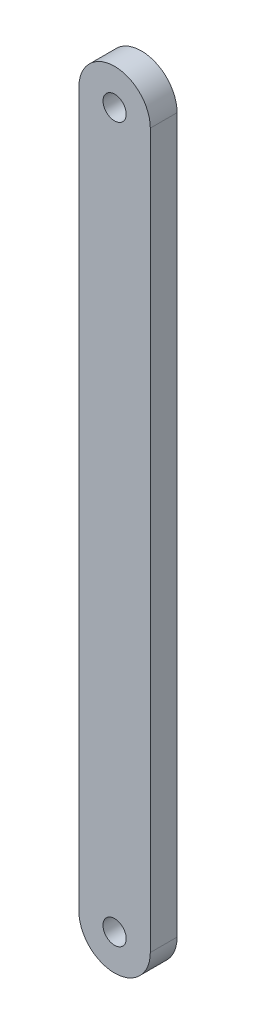
SolidWorks part; units mm, degrees
ref_plane "Front Plane" through (0, 0, 0) normal (0, 0, 1) x (1, 0, 0)
ref_plane "Top Plane" through (0, 0, 0) normal (0, 1, 0) x (1, 0, 0)
ref_plane "Right Plane" through (0, 0, 0) normal (1, 0, 0) x (0, 0, -1)
sketch "Model" plane through (0, 0, 0) normal (0, 0, 1) x (1, 0, 0)
  line L1 (47.5001, 80.0001) -> (47.5001, 0)
  line L3 (55.4999, 80.0001) -> (55.4999, 0)
  circle A0 centre (51.5001, 0) radius 1.3
  circle A1 centre (51.5001, 80) radius 1.3
  arc A2 (55.4999, 80.0001) -> (47.5001, 80.0001) centre (51.5, 80.0001) ccw
  arc A3 (47.5001, 0) -> (55.4999, 0) centre (51.5, 0) ccw
extrude "Boss-Extrude1" add sketch "Model" along normal blind 3
